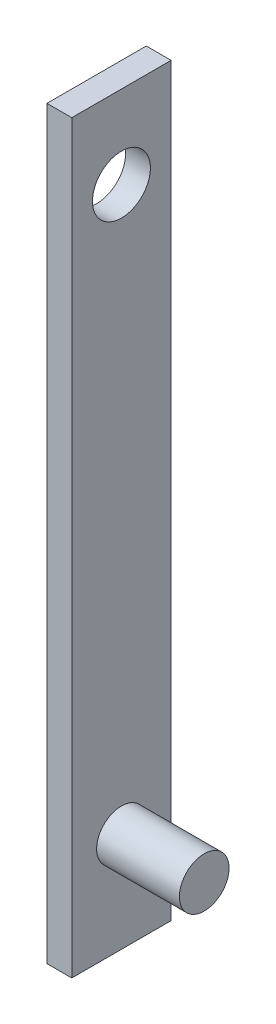
SolidWorks part; units mm, degrees
ref_plane "Front Plane" through (0, 0, 0) normal (0, 0, 1) x (1, 0, 0)
ref_plane "Top Plane" through (0, 0, 0) normal (0, 1, 0) x (1, 0, 0)
ref_plane "Right Plane" through (0, 0, 0) normal (1, 0, 0) x (0, 0, -1)
sketch "Sketch1" plane through (0, 0, 0) normal (1, 0, 0) x (0, 0, -1)
  line L1 (-6, -45) -> (6, -45)
  line L2 (-6, -45) -> (-6, 45)
  line L3 (-6, 45) -> (6, 45)
  line L4 (6, -45) -> (6, 45)
  line L5 (-6, -45) -> (6, 45) construction
  line L6 (-6, 45) -> (6, -45) construction
  point P0 (0, 0)
  dimension "D1" = 90
  dimension "D2" = 12
extrude "Boss-Extrude1" add sketch "Sketch1" along normal blind 3
sketch "Sketch2" plane through (3, 0, 0) normal (1, 0, 0) x (0, 0, -1)
  line L0 (6, 45) -> (-6, 45) construction
  circle A0 centre (0, 35) radius 3.5
  dimension "D1" = 10
extrude "Cut-Extrude1" cut sketch "Sketch2" against normal up to surface (3 mm away) up to face at (0, 0, 0)
sketch "Sketch3" plane through (3, 0, 0) normal (1, 0, 0) x (0, 0, -1)
  line L0 (6, 45) -> (-6, 45) construction
  circle A0 centre (0, -33) radius 3
  dimension "D1" = 78
extrude "Boss-Extrude2" add sketch "Sketch3" along normal blind 10
